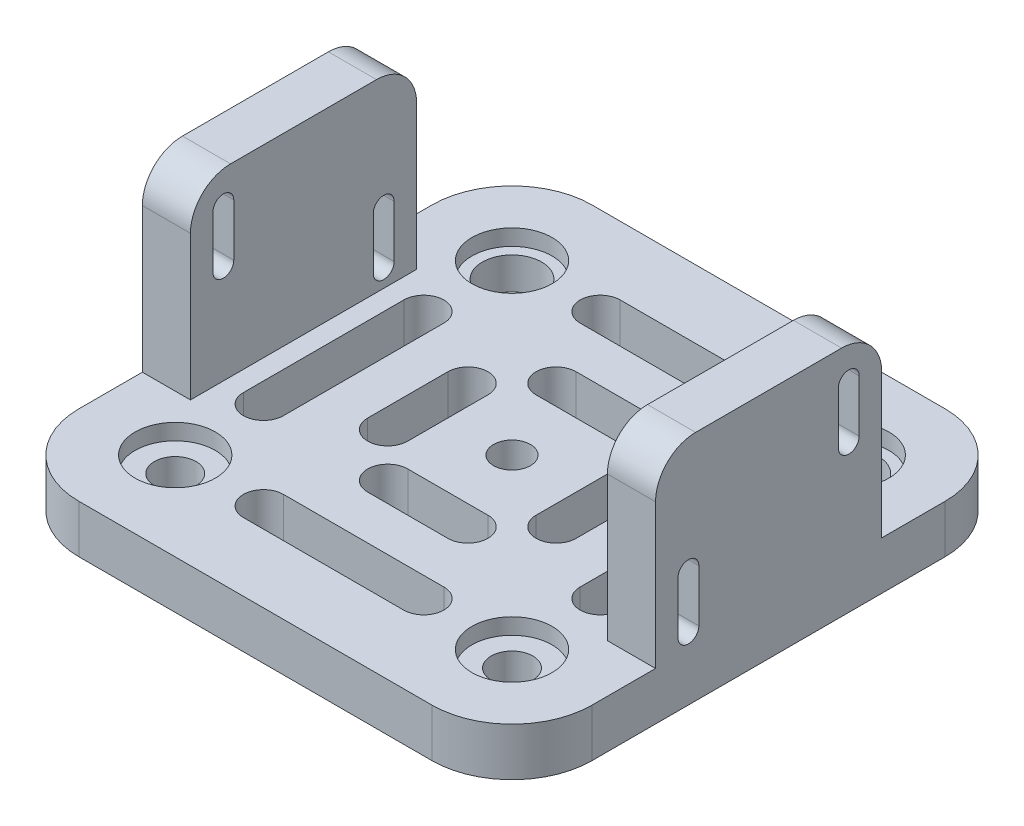
SolidWorks part; units mm, degrees
ref_plane "Спереди" through (0, 0, 0) normal (0, 0, 1) x (1, 0, 0)
ref_plane "Сверху" through (0, 0, 0) normal (0, 1, 0) x (1, 0, 0)
ref_plane "Справа" through (0, 0, 0) normal (1, 0, 0) x (0, 0, -1)
ref_plane "Plane1" through (0, 6, 0) normal (0, 1, 0) x (1, 0, 0)
sketch "Sketch1" plane through (0, 6, 0) normal (0, 1, 0) x (1, 0, 0)
  line L0 (32, 32) -> (-32, 32)
  line L1 (-32, 32) -> (-32, -32)
  line L2 (-32, 32) -> (32, -32) construction
  line L3 (32, 32) -> (-32, -32) construction
  line L4 (-32, -32) -> (32, -32)
  line L5 (32, -32) -> (32, 32)
  point P0 (0, 0)
  dimension "D1" = 64
  dimension "D2" = 64
extrude "Boss-Extrude1" add sketch "Sketch1" against normal blind 6
hole_wizard "Ø4.6 (4.6) Diameter Hole1" positions "Sketch10" profile "Sketch9" hole size "Ø4.6" standard "ANSI Metric" end condition through all
sketch "Sketch10" plane through (0, 0, 0) normal (0, -1, 0) x (-1, 0, 0)
  point P2 (0, 0)
sketch "Sketch9" plane through (0, 0, 0) normal (1, 0, 0) x (0, 0, -1)
  line L0 (0, 0) -> (0, 6)
  line L1 (0, 6) -> (2.3, 6)
  line L2 (2.3, 6) -> (2.3, 0)
  line L5 (2.3, 0) -> (0, 0)
  line L11 (0, -6.35) -> (0, 107.95) construction
  dimension "Thru Hole Dia." = 4.6
  dimension "Thru Hole Depth" = 6
hole_wizard "CBORE for M6.5 SHSS1" positions "Sketch12" profile "Sketch11" counterbore size "M6.5" standard "ANSI Metric" end condition through all
sketch "Sketch12" plane through (0, 6, 0) normal (0, 1, 0) x (1, 0, 0)
  point P0 (21, 21)
  point P9 (-21, 21)
  point P11 (0, 0)
  point P12 (0, 0)
  point P13 (0, 0)
  point P14 (0, 0)
  dimension "D1" = 21
  dimension "D2" = 21
  dimension "D3" = 21
sketch "Sketch11" plane through (21, 6, -21) normal (1, 0, 0) x (0, 0, 1)
  line L0 (0, 0) -> (0, 6)
  line L1 (0, 6) -> (3.7, 6)
  line L3 (3.7, 6) -> (3.7, 2)
  line L4 (3.7, 2) -> (5, 2)
  line L5 (5, 2) -> (5, 0)
  line L7 (5, 0) -> (0, 0)
  line L11 (0, -6.35) -> (0, 107.95) construction
  dimension "Thru Hole Dia." = 7.4
  dimension "Thru Hole Depth" = 6
  dimension "C'Bore Dia." = 10
  dimension "C'Bore Depth" = 2
hole_wizard "M10x1.0 Tapped Hole1" positions "Sketch14" profile "Sketch13" tap size "M10x1.0" standard "ANSI Metric" end condition through all
sketch "Sketch14" plane through (0, 6, 0) normal (0, 1, 0) x (1, 0, 0)
  point P0 (-21, -21)
  point P1 (-21, 21)
  point P15 (21, -21)
  point P18 (0, 0)
  point P19 (0, 0)
  point P20 (0, 0)
  point P21 (0, 0)
  dimension "D1" = 21
  dimension "D2" = 21
sketch "Sketch13" plane through (-21, 6, 21) normal (1, 0, 0) x (0, 0, 1)
  line L0 (0, 0) -> (0, 6)
  line L1 (0, 6) -> (2.6, 6)
  line L3 (2.6, 6) -> (2.6, 2)
  line L4 (2.6, 2) -> (5, 2)
  line L5 (5, 2) -> (5, 0)
  line L7 (5, 0) -> (0, 0)
  line L11 (0, -6.35) -> (0, 107.95) construction
  dimension "Thru Tap Drill Dia." = 5.2
  dimension "Thru Tap Drill Depth" = 6
  dimension "Thread Major Dia." = 10
  dimension "Thread Depth" = 2
sketch "Sketch15" plane through (0, 0, 0) normal (1, 0, 0) x (0, 0, -1)
  line L5 (-10, 18.4) -> (-10, 24.9) construction
  line L6 (-11.3, 18.4) -> (-11.3, 24.9)
  line L8 (-8.7, 18.4) -> (-8.7, 24.9)
  line L9 (0, 3.3) -> (0, -3.3) construction
  line L12 (-14.1, 0) -> (14.1, 0)
  line L13 (-14.1, 0) -> (-14.1, 29)
  line L14 (-14.1, 29) -> (14.1, 29)
  line L15 (14.1, 0) -> (14.1, 29)
  line L16 (-32, 0) -> (32, 0) construction
  line L17 (55, 6) -> (-55, 6) construction
  line L18 (10, 8.25) -> (10, 14.75) construction
  line L19 (8.7, 8.25) -> (8.7, 14.75)
  line L20 (11.3, 8.25) -> (11.3, 14.75)
  arc A0 (-11.3, 18.4) -> (-8.7, 18.4) centre (-10, 18.4) ccw
  arc A1 (-8.7, 24.9) -> (-11.3, 24.9) centre (-10, 24.9) ccw
  arc A2 (8.7, 8.25) -> (11.3, 8.25) centre (10, 8.25) ccw
  arc A3 (11.3, 14.75) -> (8.7, 14.75) centre (10, 14.75) ccw
  point P2 (-10, 21.65)
  point P16 (10, 11.5)
  point P19 (-10, 26.2)
  dimension "D4" = 1.3
  dimension "D1" = 10
  dimension "D3" = 6.5
  dimension "D2" = 15.65
  dimension "D5" = 2.8
  dimension "D6" = 2.8
  dimension "D7" = 10
  dimension "D8" = 5.5
  dimension "D9" = 2.8
extrude "Boss-Extrude4" add sketch "Sketch15" along normal blind 6 from surface at -32 starting at face at (-32, 3, 0)
sketch "Sketch16" plane through (0, 0, 0) normal (1, 0, 0) x (0, 0, -1)
  line L0 (-32, 0) -> (32, 0) construction
  line L5 (-10, 7.9) -> (-10, 14.4) construction
  line L6 (-11.3, 7.9) -> (-11.3, 14.4)
  line L7 (55, 6) -> (-55, 6) construction
  line L8 (-8.7, 7.9) -> (-8.7, 14.4)
  line L12 (-14.1, 0) -> (14.1, 0)
  line L13 (-14.1, 0) -> (-14.1, 29)
  line L14 (-14.1, 29) -> (14.1, 29)
  line L15 (14.1, 0) -> (14.1, 29)
  line L18 (10, 18.4) -> (10, 24.9) construction
  line L19 (8.7, 18.4) -> (8.7, 24.9)
  line L20 (11.3, 18.4) -> (11.3, 24.9)
  arc A0 (-11.3, 7.9) -> (-8.7, 7.9) centre (-10, 7.9) ccw
  arc A1 (-8.7, 14.4) -> (-11.3, 14.4) centre (-10, 14.4) ccw
  arc A2 (8.7, 18.4) -> (11.3, 18.4) centre (10, 18.4) ccw
  arc A3 (11.3, 24.9) -> (8.7, 24.9) centre (10, 24.9) ccw
  point P2 (-10, 11.15)
  point P16 (10, 21.65)
  point P17 (10, 26.2)
  dimension "D4" = 1.3
  dimension "D6" = 2.8
  dimension "D1" = 10
  dimension "D2" = 10
  dimension "D3" = 6.5
  dimension "D5" = 2.8
  dimension "D7" = 5.15
  dimension "D8" = 15.65
  dimension "D9" = 2.8
extrude "Boss-Extrude5" add sketch "Sketch16" against normal blind 6 from surface at 32 starting at face at (32, 3, 0)
sketch "Electromagnet" plane through (0, 6, 0) normal (0, 1, 0) x (1, 0, 0)
  circle A0 centre (0, 0) radius 17
  dimension "D1" = 34
sketch "Sketch17" plane through (0, 6, 0) normal (0, 1, 0) x (1, 0, 0)
  line L0 (10.5, -5) -> (10.5, 5) construction
  line L1 (8, -5) -> (8, 5)
  line L2 (13, -5) -> (13, 5)
  line L3 (21, -10) -> (21, 10) construction
  line L4 (18.5, -10) -> (18.5, 10)
  line L5 (23.5, -10) -> (23.5, 10)
  line L6 (-5, -10.5) -> (5, -10.5) construction
  line L7 (-5, -8) -> (5, -8)
  line L8 (-5, -13) -> (5, -13)
  line L9 (-10, -21) -> (10, -21) construction
  line L10 (-10, -18.5) -> (10, -18.5)
  line L11 (-10, -23.5) -> (10, -23.5)
  line L12 (-10.5, 5) -> (-10.5, -5) construction
  line L13 (-8, 5) -> (-8, -5)
  line L14 (-13, 5) -> (-13, -5)
  line L15 (-21, 10) -> (-21, -10) construction
  line L16 (-18.5, 10) -> (-18.5, -10)
  line L17 (-23.5, 10) -> (-23.5, -10)
  line L18 (5, 10.5) -> (-5, 10.5) construction
  line L19 (5, 8) -> (-5, 8)
  line L20 (5, 13) -> (-5, 13)
  line L21 (10, 21) -> (-10, 21) construction
  line L22 (10, 18.5) -> (-10, 18.5)
  line L23 (10, 23.5) -> (-10, 23.5)
  arc A0 (8, -5) -> (13, -5) centre (10.5, -5) ccw
  arc A1 (13, 5) -> (8, 5) centre (10.5, 5) ccw
  arc A2 (18.5, -10) -> (23.5, -10) centre (21, -10) ccw
  arc A3 (23.5, 10) -> (18.5, 10) centre (21, 10) ccw
  arc A4 (-5, -8) -> (-5, -13) centre (-5, -10.5) ccw
  arc A5 (5, -13) -> (5, -8) centre (5, -10.5) ccw
  arc A6 (-10, -18.5) -> (-10, -23.5) centre (-10, -21) ccw
  arc A7 (10, -23.5) -> (10, -18.5) centre (10, -21) ccw
  arc A8 (-8, 5) -> (-13, 5) centre (-10.5, 5) ccw
  arc A9 (-13, -5) -> (-8, -5) centre (-10.5, -5) ccw
  arc A10 (-18.5, 10) -> (-23.5, 10) centre (-21, 10) ccw
  arc A11 (-23.5, -10) -> (-18.5, -10) centre (-21, -10) ccw
  arc A12 (5, 8) -> (5, 13) centre (5, 10.5) ccw
  arc A13 (-5, 13) -> (-5, 8) centre (-5, 10.5) ccw
  arc A14 (10, 18.5) -> (10, 23.5) centre (10, 21) ccw
  arc A15 (-10, 23.5) -> (-10, 18.5) centre (-10, 21) ccw
  point P2 (10.5, 0)
  point P9 (21, 0)
  point P15 (0, 0)
  point P19 (0, -10.5)
  point P27 (0, -21)
  point P35 (-10.5, 0)
  point P41 (-21, 0)
  point P49 (0, 10.5)
  point P55 (0, 21)
  point P61 (0, 0)
  dimension "D1" = 2.5
  dimension "D6" = 2.5
  dimension "D3" = 10
  dimension "D4" = 20
  dimension "D2" = 10.5
  dimension "D5" = 4
extrude "Cut-Extrude3" cut sketch "Sketch17" against normal through all
fillet "Fillet3" radius 10 4 edges at (-32, 3, -32) (32, 3, -32) (32, 3, 32) (-32, 3, 32)
fillet "Fillet4" radius 5 4 edges at (29, 29, -14.1) (29, 29, 14.1) (-29, 29, -14.1) (-29, 29, 14.1)
equation "\"D7@Sketch15\"=\"D1@Sketch15\""
equation "\"D9@Sketch15\"=\"D5@Sketch15\""
equation "\"D6@Sketch17\"=\"D1@Sketch17\""
equation "\"D3@Sketch12\"=\"D2@Sketch12\""
